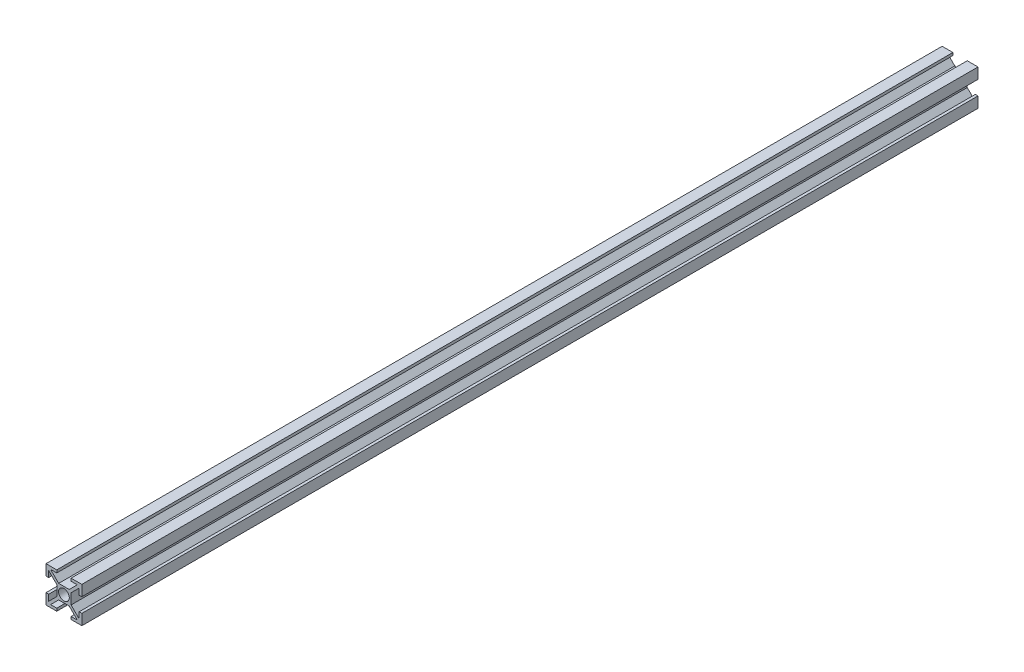
SolidWorks part; units mm, degrees
material "3.0205 (EN-AW 1200)"
ref_plane "Plano frontal" through (0, 0, 0) normal (0, 0, 1) x (1, 0, 0)
ref_plane "Plano superior" through (0, 0, 0) normal (0, 1, 0) x (1, 0, 0)
ref_plane "Plano direito" through (0, 0, 0) normal (1, 0, 0) x (0, 0, -1)
sketch "Esboço1" plane through (0, 0, 0) normal (0, 0, 1) x (1, 0, 0)
  line L0 (-2.9393, 4) -> (2.9393, 4)
  line L1 (-10, -10) -> (-4, -10)
  line L2 (-10, -10) -> (-10, -4)
  line L3 (-10, 10) -> (-4, 10)
  line L4 (10, -10) -> (10, -4)
  line L5 (-10, -10) -> (-4, -4) construction
  line L6 (-10, 10) -> (0, 0) construction
  line L7 (-7.4393, -8.5) -> (-2.9393, -4)
  line L8 (4, -10) -> (10, -10)
  line L9 (-8.5, -7.4393) -> (-4, -2.9393)
  line L10 (-8.5, 7.4393) -> (-4, 2.9393)
  line L11 (-7.4393, -8.5) -> (-4, -8.5)
  line L12 (-8.5, -7.4393) -> (-8.5, -4)
  line L13 (-7.4393, 8.5) -> (-4, 8.5)
  line L14 (8.5, -7.4393) -> (8.5, -4)
  line L17 (-4, 10) -> (-4, 8.5)
  line L18 (4, -8.5) -> (7.4393, -8.5)
  line L19 (-10, -4) -> (-8.5, -4)
  line L20 (4, 10) -> (4, 8.5)
  line L21 (-10, 4) -> (-8.5, 4)
  line L22 (-4, 2.9393) -> (-4, -2.9393)
  line L23 (-4, -8.5) -> (-4, -10)
  line L24 (-8.5, 4) -> (-8.5, 7.4393)
  line L25 (-10, 4) -> (-10, 10)
  line L26 (-7.4393, 8.5) -> (-2.9393, 4)
  line L27 (4, 8.5) -> (7.4393, 8.5)
  line L28 (-2.9393, -4) -> (2.9393, -4)
  line L29 (4, 10) -> (10, 10)
  line L30 (4, -8.5) -> (4, -10)
  line L31 (10, 4) -> (10, 10)
  line L32 (8.5, 4) -> (8.5, 7.4393)
  line L33 (-10.5303, -9.4697) -> (9.4697, 10.5303) construction
  line L34 (8.5, 4) -> (10, 4)
  line L35 (8.5, -4) -> (10, -4)
  line L36 (-10, -10) -> (10, 10) construction
  line L37 (4, 2.9393) -> (4, -2.9393)
  line L38 (-9.4697, -10.5303) -> (10.5303, 9.4697) construction
  line L40 (2.9393, -4) -> (7.4393, -8.5)
  line L41 (4, -4) -> (10, -10) construction
  line L43 (4, -2.9393) -> (8.5, -7.4393)
  line L44 (4, 0) -> (10, 0) construction
  line L45 (4, 2.9393) -> (8.5, 7.4393)
  line L47 (4, 4) -> (10, 10) construction
  line L48 (2.9393, 4) -> (7.4393, 8.5)
  circle A0 centre (0, 0) radius 3
  point P0 (0, 0)
  point P14 (-4.0323, -3.9672)
  dimension "D5" = 6
  dimension "D1" = 0.75
  dimension "D3" = 1.5
  dimension "D4" = 20
  dimension "D6" = 8
  dimension "D7" = 20
  dimension "D9" = 1.5
  dimension "D2" = 8
extrude "Ressalto-extrusão1" add sketch "Esboço1" along normal blind 500
